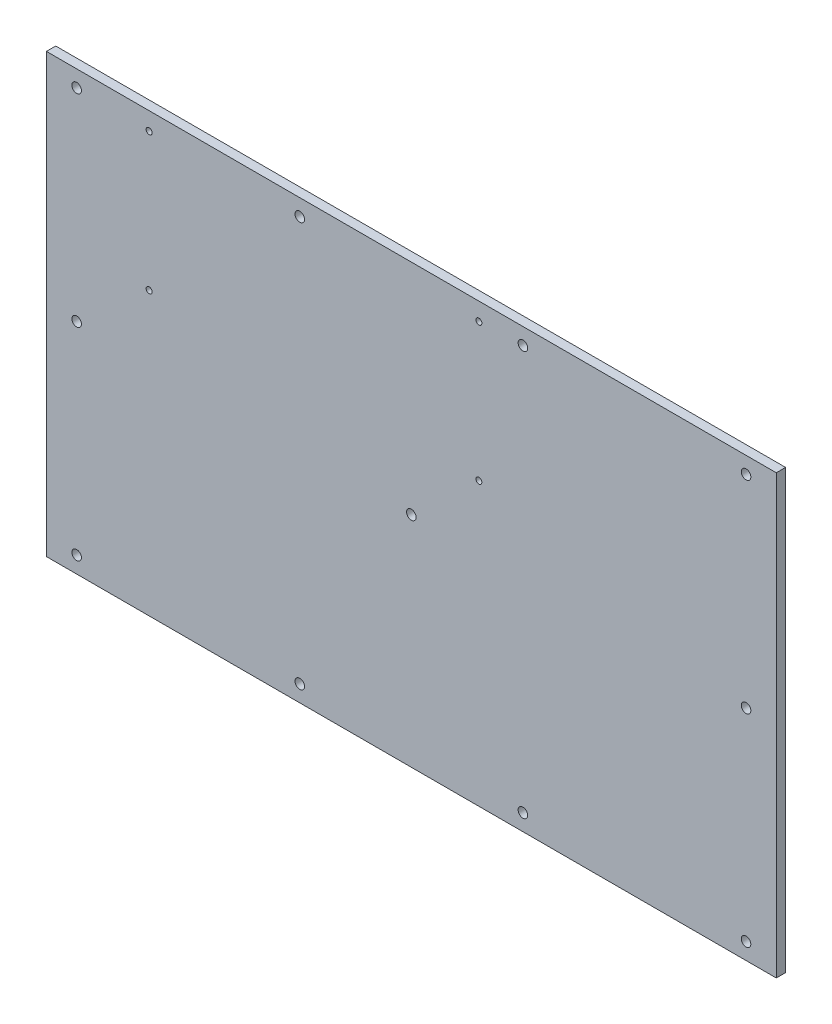
SolidWorks part; units mm, degrees
ref_plane "Front Plane" through (0, 0, 0) normal (0, 0, 1) x (1, 0, 0)
ref_plane "Top Plane" through (0, 0, 0) normal (0, 1, 0) x (1, 0, 0)
ref_plane "Right Plane" through (0, 0, 0) normal (1, 0, 0) x (0, 0, -1)
sketch "Sketch1" plane through (0, 0, 0) normal (0, 0, 1) x (1, 0, 0)
  line L1 (-124.46, 74.6125) -> (124.46, 74.6125)
  line L2 (-124.46, 74.6125) -> (-124.46, -74.6125)
  line L3 (-124.46, -74.6125) -> (124.46, -74.6125)
  line L4 (124.46, 74.6125) -> (124.46, -74.6125)
  line L5 (-124.46, 74.6125) -> (124.46, -74.6125) construction
  line L6 (-124.46, -74.6125) -> (124.46, 74.6125) construction
  point P0 (0, 0)
  dimension "D1" = 248.92
  dimension "D2" = 149.225
extrude "Boss-Extrude1" add sketch "Sketch1" along normal blind 3.175 contours L1 L4 L3 L2
hole_wizard "#4 Clearance Hole1" positions "Sketch3" profile "Sketch2" hole size "#4" standard "ANSI Inch"
sketch "Sketch3" plane through (0, 0, 0) normal (0, 0, -1) x (-1, 0, 0)
  line L1 (114.1476, -68.9864) -> (-114.1476, -68.9864)
  line L2 (114.1476, -68.9864) -> (114.1476, 68.9864)
  line L3 (114.1476, 68.9864) -> (-114.1476, 68.9864)
  line L4 (-114.1476, -68.9864) -> (-114.1476, 68.9864)
  line L5 (114.1476, -68.9864) -> (-114.1476, 68.9864) construction
  line L6 (114.1476, 68.9864) -> (-114.1476, -68.9864) construction
  line L7 (38.0492, -68.9864) -> (38.0492, 68.9864) construction
  line L9 (-38.0492, -68.9864) -> (-38.0492, 68.9864) construction
  point P0 (114.1476, -68.9864)
  point P2 (-114.1476, -68.9864)
  point P4 (-114.1476, 68.9864)
  point P6 (114.1476, 68.9864)
  point P8 (114.1476, 0)
  point P10 (-114.1476, 0)
  point P12 (38.0492, 68.9864)
  point P14 (-38.0492, 68.9864)
  point P16 (-38.0492, -68.9864)
  point P18 (38.0492, -68.9864)
  point P21 (0, 0)
  dimension "D1" = 137.9728
  dimension "D2" = 228.2952
  dimension "D3" = 76.0984
  dimension "D4" = 76.0984
sketch "Sketch2" plane through (-114.1476, -68.9864, 0) normal (1, 0, 0) x (0, 1, 0)
  line L0 (0, 0) -> (0, 57.3686)
  line L1 (0, 57.3686) -> (1.6319, 56.388)
  line L2 (1.6319, 56.388) -> (1.6319, 0)
  line L5 (1.6319, 0) -> (0, 0)
  line L10 (0, 57.3686) -> (-1.632, 56.388) construction
  line L11 (0, -6.35) -> (0, 107.95) construction
  dimension "Hole Dia." = 3.2639
  dimension "Hole Depth" = 56.388
  dimension "Drill Angle" = 118
sketch "Sketch6" plane through (0, 0, 0) normal (0, 0, -1) x (-1, 0, 0)
  line L0 (52.7304, 72.9615) -> (52.7304, 77.4871)
  line L1 (94.1324, 9.4615) -> (-27.7876, 9.4615)
  line L2 (94.1324, 9.4615) -> (94.1324, 72.9615)
  line L3 (94.1324, 72.9615) -> (-27.7876, 72.9615)
  line L4 (-27.7876, 9.4615) -> (-27.7876, 72.9615)
  line L5 (94.1324, 9.4615) -> (-27.7876, 72.9615) construction
  line L6 (94.1324, 72.9615) -> (-27.7876, 9.4615) construction
  line L7 (124.46, -74.6125) -> (-124.46, -74.6125) construction
  line L9 (52.7304, 77.4871) -> (15.9004, 77.4871)
  line L10 (15.9004, 77.4871) -> (15.9004, 72.9615)
  line L11 (34.3154, 77.4871) -> (34.3154, 72.9615) construction
  line L12 (42.5851, 9.4615) -> (42.5851, 17.4525)
  line L13 (89.4384, 19.3575) -> (89.4384, 23.5743)
  line L14 (89.4384, 23.5743) -> (94.1324, 23.5743)
  line L16 (124.46, 74.6125) -> (124.46, -74.6125) construction
  point P0 (33.1724, 41.2115)
  dimension "D1" = 121.92
  dimension "D2" = 63.5
  dimension "D3" = 84.074
  dimension "D4" = 30.3276
  dimension "D5" = 36.83
  dimension "D6" = 4.5256
  dimension "D7" = 59.817
hole_wizard "#4-40 Tapped Hole1" positions "Sketch5" profile "Sketch4" tap size "#4-40" standard "ANSI Inch"
sketch "Sketch5" plane through (0, 0, 0) normal (0, 0, -1) x (-1, 0, 0)
  line L7 (33.1724, 21.5773) -> (33.1724, 68.5673)
  line L9 (89.4334, 68.5673) -> (-23.0378, 68.5673)
  line L11 (89.4334, 21.5773) -> (-23.0378, 21.5773)
  line L13 (-27.7876, 9.4615) -> (-27.7876, 72.9615) construction
  line L14 (94.1324, 9.4615) -> (94.1324, 72.9615) construction
  line L15 (94.1324, 72.9615) -> (-27.7876, 72.9615) construction
  line L16 (94.1324, 9.4615) -> (-27.7876, 9.4615) construction
  point P0 (-23.0378, 21.5773)
  point P2 (-23.0378, 68.5673)
  point P4 (89.4334, 68.5673)
  point P6 (89.4334, 21.5773)
  dimension "D1" = 4.7498
  dimension "D2" = 4.699
  dimension "D3" = 4.3942
  dimension "D4" = 12.1158
  dimension "D5" = 4.7498
  dimension "D6" = 4.699
sketch "Sketch4" plane through (23.0378, 21.5773, 0) normal (1, 0, 0) x (0, 1, 0)
  line L0 (0, 0) -> (0, 8.2305)
  line L1 (0, 8.2305) -> (1.016, 7.62)
  line L2 (1.016, 7.62) -> (1.016, 0)
  line L5 (1.016, 0) -> (0, 0)
  line L10 (0, 8.2305) -> (-1.016, 7.62) construction
  line L11 (0, -6.35) -> (0, 107.95) construction
  dimension "Tap Drill Dia." = 2.032
  dimension "Tap Drill Depth" = 7.62
  dimension "Drill Angle" = 118
cosmetic thread "Hole Thread1" parameters "D1"=3.175, "D2"=2.8448
cosmetic thread "Hole Thread2" parameters "D1"=3.175, "D2"=2.8448
cosmetic thread "Hole Thread3" parameters "D1"=3.175, "D2"=2.8448
cosmetic thread "Hole Thread4" parameters "D1"=3.175, "D2"=2.8448
